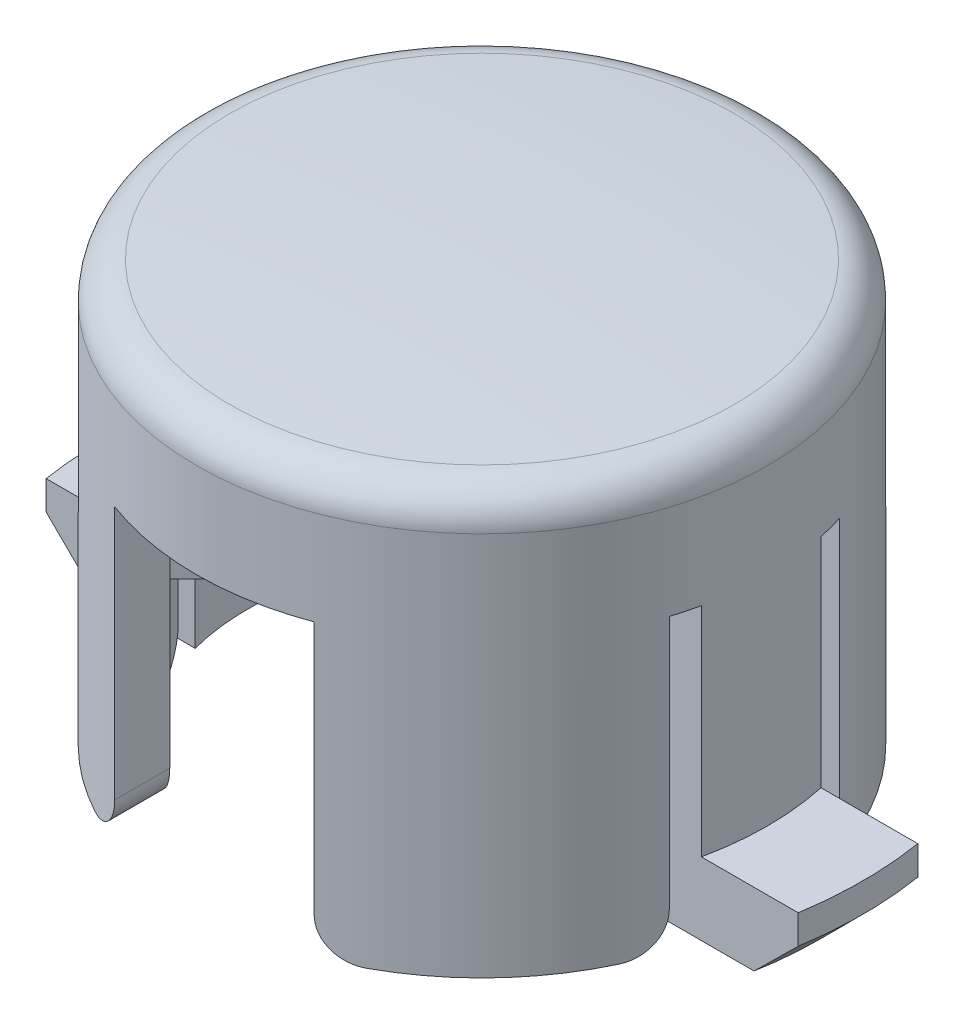
SolidWorks part; units mm, degrees
ref_plane "Front" through (0, 0, 0) normal (0, 0, 1) x (1, 0, 0)
ref_plane "Top" through (0, 0, 0) normal (0, 1, 0) x (1, 0, 0)
ref_plane "Right" through (0, 0, 0) normal (1, 0, 0) x (0, 0, -1)
sketch "Sketch1" plane through (0, 0, 0) normal (0, 0, 1) x (1, 0, 0)
  line L0 (0, 0) -> (0, 6.0399)
  line L1 (0, 6.0399) -> (21.0862, 6.0399) construction
  line L2 (0, 3.9609) -> (8.222, 3.9609)
  line L3 (10, 4.4214) -> (10, -9.0477)
  line L4 (8.222, 3.9609) -> (8.222, -9.0477)
  line L5 (8.222, -9.0477) -> (10, -9.0477)
  arc A0 (0, 6.0399) -> (8.8312, 5.6874) centre (0, -104.7583) cw
  arc A1 (10, 4.4214) -> (8.8312, 5.6874) centre (8.73, 4.4214) ccw
  dimension "D1" = 1.27
  dimension "D2" = 10
  dimension "D3" = 1.778
  dimension "D4" = 15.0876
revolve "dome/base" add sketch "Sketch1" angle 360 about L0
sketch "Sketch2" plane through (0, -9.0477, 0) normal (0, -1, 0) x (1, 0, 0)
  line L0 (-3.4925, 0) -> (3.4925, 0) construction
  line L1 (-3.4925, 16.1782) -> (3.4925, 16.1782)
  line L2 (-3.4925, 16.1782) -> (-3.4925, -16.1782)
  line L3 (-3.4925, -16.1782) -> (3.4925, -16.1782)
  line L4 (3.4925, 16.1782) -> (3.4925, -16.1782)
  line L5 (0, 2.0955) -> (0, 0) construction
  line L6 (-20.4861, 2.9845) -> (20.4861, 2.9845)
  line L7 (-20.4861, 2.9845) -> (-20.4861, 2.0955)
  line L8 (-20.4861, 2.0955) -> (20.4861, 2.0955)
  line L9 (20.4861, 2.9845) -> (20.4861, 2.0955)
  line L10 (-20.4861, -2.9845) -> (-20.4861, -2.0955)
  line L11 (-20.4861, -2.0955) -> (20.4861, -2.0955)
  line L12 (20.4861, -2.9845) -> (20.4861, -2.0955)
  line L13 (-20.4861, -2.9845) -> (20.4861, -2.9845)
  point P6 (0, 0)
  dimension "D1" = 6.985
  dimension "D2" = 0.889
  dimension "D3" = 5.969
extrude "cutout" cut sketch "Sketch2" against normal blind 10.16 contours L6 L9 L8 L7 | L11 L12 L13 L10 | L4 L3 L2 L1
sketch "Sketch3" plane through (0, -9.0477, 0) normal (0, -1, 0) x (1, 0, 0)
  line L0 (-9.778, -2.0955) -> (-13.1693, -2.0955)
  line L1 (-9.778, 2.0955) -> (-13.1693, 2.0955)
  line L2 (-9.778, 2.0955) -> (-7.9505, 2.0955) construction
  line L3 (-9.778, -2.0955) -> (-7.9505, -2.0955) construction
  line L4 (0, -13.335) -> (0, 13.335) construction
  line L5 (9.778, 2.0955) -> (13.1693, 2.0955)
  line L6 (9.778, -2.0955) -> (13.1693, -2.0955)
  circle A0 centre (0, 0) radius 13.335
  arc A1 (-9.778, 2.0955) -> (-9.778, -2.0955) centre (0, 0) ccw construction
  arc A2 (9.778, -2.0955) -> (9.778, 2.0955) centre (0, 0) ccw construction
  arc A3 (9.778, -2.0955) -> (9.778, 2.0955) centre (0, 0) ccw
  arc A4 (-9.778, 2.0955) -> (-9.778, -2.0955) centre (0, 0) ccw
  point P13 (-10, 0)
  arc M2 (-9.778, 2.0955) -> (-9.778, -2.0955) centre (0, 0) ccw
  dimension "D1" = 26.67
extrude "tab" add sketch "Sketch3" against normal blind 2.54 contours L1 A0 L0 M2 | A3 L6 A0 L5
chamfer "tab chmf" distance 1.524 angle 45 2 edges at (13.335, -9.0477, 0) (-13.335, -9.0477, 0)
sketch "Sketch5" plane through (0, 3.9609, 0) normal (0, -1, 0) x (1, 0, 0)
  line L0 (0, 0.7184) -> (-6.1619, -5.4435)
  line L1 (-5.4435, -6.1619) -> (0, -0.7184)
  line L2 (0, 0) -> (0, -8.222) construction
  line L3 (0, -0.7184) -> (0, 0.7184) construction
  line L4 (-6.1619, 5.4435) -> (-0.7184, 0)
  line L5 (0.7184, 0) -> (-5.4435, 6.1619)
  line L6 (5.4435, 6.1619) -> (0, 0.7184)
  line L7 (0, -0.7184) -> (6.1619, 5.4435)
  line L8 (6.1619, -5.4435) -> (0.7184, 0)
  line L9 (-0.7184, 0) -> (5.4435, -6.1619)
  circle A0 centre (0, 0) radius 8.222 construction
  circle A1 centre (0, 0) radius 8.222
  point P7 (0, 0)
  circle M1 centre (0, 0) radius 8.222
  dimension "D1" = 1.016
  dimension "D3" = 45
extrude "cross" add sketch "Sketch5" along normal blind 7.62 contours L9 L0 L1 M1 | L7 L9 L8 M1 | L5 L7 L6 M1 | L0 L9 L7 L5 | L0 L5 L4 M1
sketch "Sketch4" plane through (0, 3.9609, 0) normal (0, -1, 0) x (1, 0, 0)
  line L0 (-1.651, 0) -> (1.651, 0) construction
  line L1 (-1.651, -3.8481) -> (1.651, -3.8481)
  line L2 (-1.651, -3.8481) -> (-1.651, 3.8481)
  line L3 (-1.651, 3.8481) -> (1.651, 3.8481)
  line L4 (1.651, -3.8481) -> (1.651, 3.8481)
  point P6 (0, 0)
  dimension "D1" = 3.302
  dimension "D2" = 7.6962
extrude "box" add sketch "Sketch4" along normal offset from surface (13.0594 mm away) 0.0508 up to face at (-6.3399, -9.0477, -5.9713) offset beyond the face yes
sketch "Sketch6" plane through (0, -9.0985, 0) normal (0, -1, 0) x (1, 0, 0)
  line L8 (0.889, 3.0861) -> (-0.889, 3.0861)
  line L9 (-0.889, 3.0861) -> (-0.889, -3.0861)
  line L10 (-0.889, -3.0861) -> (0.889, -3.0861)
  line L11 (0.889, -3.0861) -> (0.889, 3.0861)
  line L12 (0.889, 3.0861) -> (-0.889, 3.0861)
  line L13 (-0.889, 3.0861) -> (-0.889, -3.0861)
  line L14 (-0.889, -3.0861) -> (0.889, -3.0861)
  line L15 (0.889, -3.0861) -> (0.889, 3.0861)
  dimension "D1" = 0.762
extrude "boxcut" cut sketch "Sketch6" against normal up to surface (13.0594 mm away) up to face at (0, 3.9609, -4.4698)
fillet "Fillet1" radius 1.27 8 edges at (3.4925, -9.0477, 8.4068) (3.4925, -9.0477, -8.4068) (-3.4925, -9.0477, 8.4068) (-3.4925, -9.0477, -8.4068) (-8.6027, -9.0477, -2.9845) (8.6027, -9.0477, -2.9845) (8.6027, -9.0477, 2.9845) (-8.6027, -9.0477, 2.9845)
